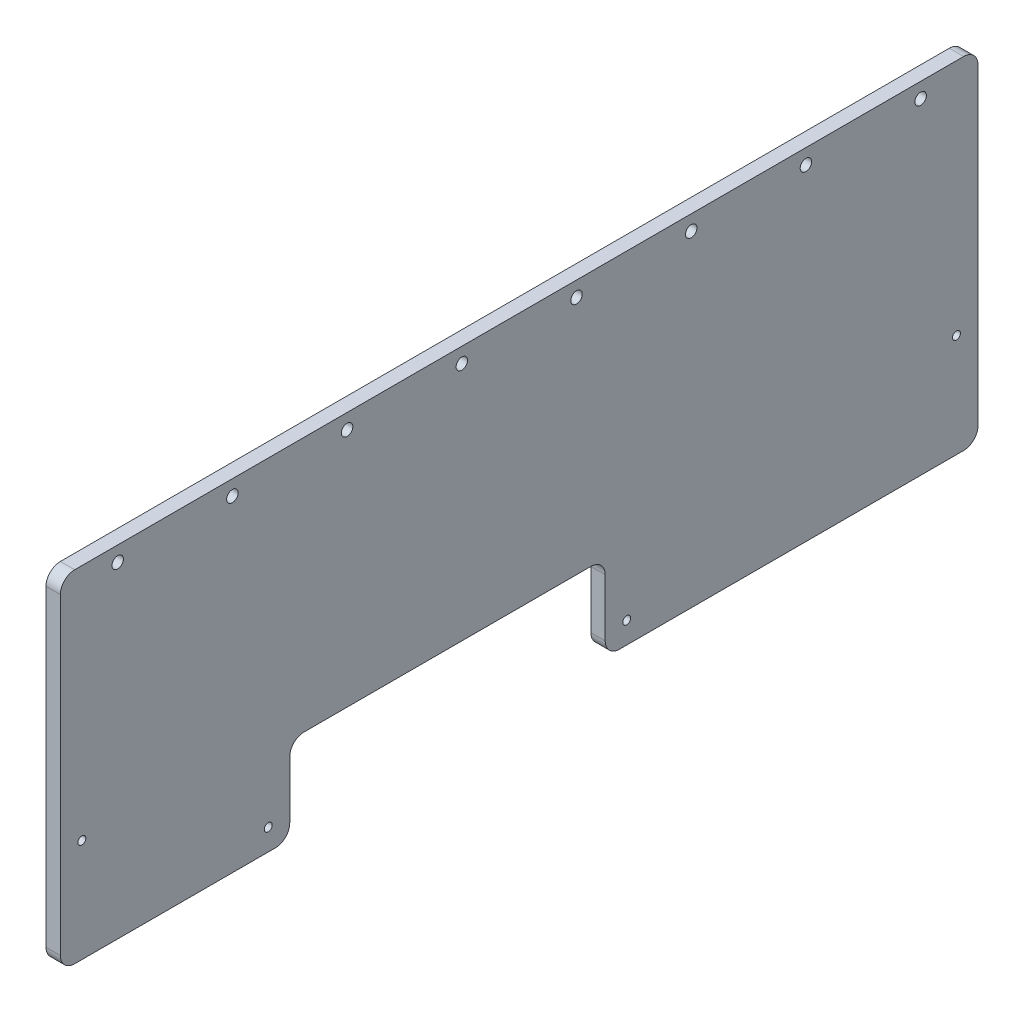
SolidWorks part; units mm, degrees
material "Acrylic (Medium-high impact)"
ref_plane "Front Plane" through (0, 0, 0) normal (0, 0, 1) x (1, 0, 0)
ref_plane "Top Plane" through (0, 0, 0) normal (0, 1, 0) x (1, 0, 0)
ref_plane "Right Plane" through (0, 0, 0) normal (1, 0, 0) x (0, 0, -1)
sketch "Sketch2" plane through (0, 0, 0) normal (1, 0, 0) x (0, 0, -1)
  line L0 (0, 0) -> (0, 294.4501)
  line L1 (0, 294.4501) -> (215.9, 419.1)
  line L2 (215.9, 419.1) -> (431.8, 419.1)
  line L3 (431.8, 419.1) -> (431.8, 0)
  line L4 (431.8, 0) -> (241.3, 0)
  line L5 (241.3, 0) -> (241.3, 38.1)
  line L6 (241.3, 38.1) -> (127, 38.1)
  line L7 (127, 38.1) -> (127, 0)
  line L8 (127, 0) -> (0, 0)
  dimension "D1" = 431.8
  dimension "D2" = 419.1
  dimension "D3" = 127
  dimension "D4" = 114.3
  dimension "D5" = 38.1
  dimension "D6" = 215.9
  dimension "D7" = 150
extrude "Boss-Extrude1" add sketch "Sketch2" along normal blind 6.35 contours L1 L2 L3 L4 L5 L6 L7 L8 L0
sketch "Sketch3" plane through (6.35, 0, 0) normal (1, 0, 0) x (0, 0, -1)
  line L0 (0, 38.1) -> (431.8, 38.1) construction
  line L1 (0, 0) -> (0, 294.4501) construction
  line L2 (431.8, 419.1) -> (431.8, 0) construction
  circle A0 centre (63.5, 38.1) radius 3.9687
  circle A1 centre (368.3, 38.1) radius 3.9688
  dimension "D4" = 7.9375
  dimension "D5" = 7.9375
  dimension "D1" = 38.1
  dimension "D2" = 63.5
  dimension "D3" = 63.5
extrude "Cut-Extrude1" cut sketch "Sketch3" against normal through all
sketch "Sketch4" plane through (6.35, 0, 0) normal (1, 0, 0) x (0, 0, -1)
  line L0 (431.8, 419.1) -> (431.8, 0) construction
  line L1 (215.9, 419.1) -> (431.8, 419.1) construction
  line L2 (393.7, 400.05) -> (393.7, 19.05) construction
  line L4 (393.7, 400.05) -> (330.2, 400.05) construction
  line L5 (330.2, 400.05) -> (330.2, 19.05) construction
  line L6 (330.2, 400.05) -> (330.2, 19.05) construction
  line L7 (330.2, 400.05) -> (323.5506, 19.108) construction
  circle A0 centre (393.7, 400.05) radius 3.175 construction
  circle A1 centre (393.7, 19.05) radius 3.175 construction
  circle A2 centre (323.5506, 19.108) radius 3.175 construction
  circle A3 centre (316.9033, 19.2821) radius 3.175 construction
  circle A4 centre (330.2, 400.05) radius 3.175 construction
  circle A5 centre (330.2, 19.05) radius 3.175 construction
  circle A6 centre (310.26, 19.5721) radius 3.175 construction
  circle A7 centre (303.6228, 19.9781) radius 3.175 construction
  circle A8 centre (296.9937, 20.4998) radius 3.175 construction
  circle A9 centre (290.3747, 21.1372) radius 3.175 construction
  circle A10 centre (283.7678, 21.8899) radius 3.175 construction
  circle A11 centre (277.175, 22.7579) radius 3.175 construction
  circle A12 centre (270.5985, 23.7407) radius 3.175 construction
  dimension "D1" = 6.35
  dimension "D2" = 38.1
  dimension "D3" = 19.05
  dimension "D4" = 381
  dimension "D5" = 10
  dimension "D6" = 1
  dimension "D7" = 101.6
sketch "Sketch5" plane through (6.35, 0, 0) normal (1, 0, 0) x (0, 0, -1)
  line L0 (431.8, 419.1) -> (431.8, 0) construction
  line L1 (431.8, 12.7) -> (425.45, 12.7)
  line L2 (431.8, 12.7) -> (431.8, 25.4)
  line L3 (431.8, 25.4) -> (425.45, 25.4)
  line L4 (425.45, 12.7) -> (425.45, 25.4)
  line L5 (431.8, 0) -> (241.3, 0) construction
  dimension "D1" = 6.35
  dimension "D2" = 12.7
  dimension "D3" = 12.7
extrude "Cut-Extrude3" cut sketch "Sketch5" against normal through all
pattern_linear "LPattern1" count 16 spacing 25.4 along (0, 1, 0) of "Cut-Extrude3"
sketch "Sketch6" plane through (6.35, 0, 0) normal (1, 0, 0) x (0, 0, -1)
  line L0 (0, 0) -> (0, 294.4501) construction
  line L1 (0, 12.7) -> (6.35, 12.7)
  line L2 (0, 12.7) -> (0, 25.4)
  line L3 (0, 25.4) -> (6.35, 25.4)
  line L4 (6.35, 12.7) -> (6.35, 25.4)
  line L5 (425.45, 12.7) -> (431.8, 12.7) construction
  line L6 (425.45, 25.4) -> (425.45, 12.7) construction
  line L7 (127, 0) -> (0, 0) construction
  dimension "D1" = 12.7
extrude "Cut-Extrude4" cut sketch "Sketch6" against normal through all
pattern_linear "LPattern2" count 11 spacing 25.4 along (0, 1, 0) of "Cut-Extrude4"
sketch "Sketch7" plane through (6.35, 0, 0) normal (1, 0, 0) x (0, 0, -1)
  line L0 (127, 38.1) -> (127, 0) construction
  line L1 (127, 12.7) -> (120.65, 12.7)
  line L2 (127, 12.7) -> (127, 25.4)
  line L3 (127, 25.4) -> (120.65, 25.4)
  line L4 (120.65, 12.7) -> (120.65, 25.4)
  line L5 (241.3, 38.1) -> (127, 38.1) construction
  line L6 (127, 38.1) -> (139.7, 38.1)
  line L7 (127, 38.1) -> (127, 44.45)
  line L8 (127, 44.45) -> (139.7, 44.45)
  line L9 (139.7, 38.1) -> (139.7, 44.45)
  line L10 (241.3, 0) -> (241.3, 38.1) construction
  line L11 (152.4, 38.1) -> (165.1, 38.1)
  line L12 (152.4, 38.1) -> (152.4, 44.45)
  line L13 (152.4, 44.45) -> (165.1, 44.45)
  line L14 (165.1, 38.1) -> (165.1, 44.45)
  line L15 (177.8, 38.1) -> (190.5, 38.1)
  line L16 (177.8, 38.1) -> (177.8, 44.45)
  line L17 (177.8, 44.45) -> (190.5, 44.45)
  line L18 (190.5, 38.1) -> (190.5, 44.45)
  line L19 (241.3, 25.4) -> (247.65, 25.4)
  line L20 (241.3, 25.4) -> (241.3, 12.7)
  line L21 (241.3, 12.7) -> (247.65, 12.7)
  line L22 (247.65, 25.4) -> (247.65, 12.7)
  line L23 (0, 12.7) -> (6.35, 12.7) construction
  line L24 (6.35, 12.7) -> (6.35, 25.4) construction
  line L25 (127, 0) -> (0, 0) construction
  line L26 (431.8, 0) -> (241.3, 0) construction
  line L27 (203.2, 44.45) -> (215.9, 44.45)
  line L28 (203.2, 44.45) -> (203.2, 38.1)
  line L29 (203.2, 38.1) -> (215.9, 38.1)
  line L30 (215.9, 44.45) -> (215.9, 38.1)
  line L32 (241.3, 38.1) -> (228.6, 38.1)
  line L33 (241.3, 38.1) -> (241.3, 44.45)
  line L34 (241.3, 44.45) -> (228.6, 44.45)
  line L35 (228.6, 38.1) -> (228.6, 44.45)
  dimension "D1" = 12.7
  dimension "D2" = 12.7
  dimension "D4" = 12.7
  dimension "D5" = 12.7
  dimension "D6" = 12.7
extrude "Cut-Extrude5" cut sketch "Sketch7" against normal through all
sketch "Sketch8" plane through (6.35, 0, 0) normal (1, 0, 0) x (0, 0, -1)
  line L0 (201.9351, 411.0373) -> (212.9336, 417.3873)
  line L1 (201.9351, 411.0373) -> (205.1101, 405.5381)
  line L2 (212.9336, 417.3873) -> (216.1086, 411.8881)
  line L3 (205.1101, 405.5381) -> (216.1086, 411.8881)
  line L4 (0, 294.4501) -> (215.9, 419.1) construction
  line L5 (6.35, 279.4) -> (0, 279.4) construction
  line L6 (6.35, 266.7) -> (6.35, 279.4) construction
  line L7 (216.1086, 411.8881) -> (7.1367, 291.2381) construction
  line L8 (6.35, 279.4) -> (6.35, 292.1) construction
  line L9 (215.9, 412.75) -> (215.6832, 412.6248) construction
  line L10 (7.1367, 291.2381) -> (3.9617, 296.7373) construction
  line L11 (6.35, 292.1) -> (6.5668, 292.2252) construction
  line L12 (215.9, 419.1) -> (215.9, 412.75) construction
  line L13 (215.9, 419.1) -> (431.8, 419.1) construction
  dimension "D1" = 215.9
  dimension "D2" = 241.3
  dimension "D3" = 6.35
extrude "Cut-Extrude6" cut sketch "Sketch8" against normal through all
pattern_linear "LPattern3" count 10 spacing 25.4 along (0, -0.5, 0.866) of "Cut-Extrude6"
sketch "Sketch9" plane through (6.35, 0, 0) normal (1, 0, 0) x (0, 0, -1)
  line L0 (215.9, 419.1) -> (431.8, 419.1) construction
  line L1 (419.1, 419.1) -> (406.4, 419.1)
  line L2 (419.1, 419.1) -> (419.1, 412.75)
  line L3 (419.1, 412.75) -> (406.4, 412.75)
  line L4 (406.4, 419.1) -> (406.4, 412.75)
  line L5 (431.8, 406.4) -> (425.45, 406.4) construction
  line L6 (425.45, 406.4) -> (425.45, 393.7) construction
  line L7 (431.8, 419.1) -> (431.8, 406.4) construction
  dimension "D1" = 12.7
extrude "Cut-Extrude7" cut sketch "Sketch9" against normal through all
pattern_linear "LPattern4" count 8 spacing 25.4 along (0, 0, 1) of "Cut-Extrude7"
sketch "Sketch10" plane through (6.35, 0, 0) normal (1, 0, 0) x (0, 0, -1)
  line L0 (127, 0) -> (0, 0) construction
  line L1 (146.05, 273.05) -> (222.25, 273.05) construction
  line L2 (146.05, 273.05) -> (146.05, 57.15) construction
  line L3 (146.05, 57.15) -> (222.25, 57.15) construction
  line L4 (222.25, 273.05) -> (222.25, 57.15) construction
  line L5 (146.05, 273.05) -> (19.05, 273.05) construction
  line L6 (146.05, 273.05) -> (146.05, 247.65) construction
  line L7 (146.05, 247.65) -> (19.05, 247.65) construction
  line L8 (19.05, 273.05) -> (19.05, 247.65) construction
  line L9 (0, 254) -> (0, 266.7) construction
  line L10 (127, 44.45) -> (127, 25.4) construction
  line L11 (241.3, 25.4) -> (241.3, 44.45) construction
  line L12 (152.4, 38.1) -> (139.7, 38.1) construction
  circle A0 centre (222.25, 273.05) radius 3.175
  circle A1 centre (222.25, 57.15) radius 3.175
  circle A2 centre (146.05, 57.15) radius 3.175
  circle A3 centre (146.05, 273.05) radius 3.175
  circle A4 centre (19.05, 273.05) radius 3.175 construction
  circle A5 centre (19.05, 247.65) radius 3.175 construction
  circle A6 centre (146.05, 247.65) radius 3.175 construction
  dimension "D4" = 6.35
  dimension "D1" = 273.05
  dimension "D2" = 19.05
  dimension "D3" = 247.65
  dimension "D5" = 19.05
  dimension "D6" = 19.05
  dimension "D7" = 19.05
extrude "Cut-Extrude8" cut sketch "Sketch10" against normal through all
sketch "Sketch11" plane through (6.35, 0, 0) normal (1, 0, 0) x (0, 0, -1)
  line L0 (127, 0) -> (0, 0) construction
  line L1 (0, 254) -> (0, 266.7) construction
  line L5 (241.3, 0) -> (241.3, 12.7) construction
  line L6 (177.8, 38.1) -> (165.1, 38.1) construction
  line L7 (38.1, 260.35) -> (266.7, 260.35) construction
  line L8 (266.7, 260.35) -> (266.7, 63.5) construction
  circle A0 centre (38.1, 260.35) radius 3.9688
  circle A1 centre (266.7, 63.5) radius 3.9688 construction
  circle A2 centre (266.7, 260.35) radius 3.9688
  dimension "D3" = 7.9375
  dimension "D1" = 260.35
  dimension "D2" = 38.1
  dimension "D4" = 25.4
  dimension "D5" = 25.4
extrude "Cut-Extrude9" cut sketch "Sketch11" against normal through all
sketch "Sketch12" plane through (6.35, 0, 0) normal (1, 0, 0) x (0, 0, -1)
  line L0 (127, 50.8) -> (127, 38.1)
  line L1 (120.65, 25.4) -> (127, 25.4)
  line L2 (120.65, 25.4) -> (120.65, 12.7)
  line L3 (120.65, 12.7) -> (127, 12.7)
  line L4 (127, 25.4) -> (127, 12.7)
  line L5 (120.65, 50.8) -> (127, 50.8)
  line L6 (120.65, 50.8) -> (120.65, 38.1)
  line L7 (120.65, 38.1) -> (127, 38.1)
  line L8 (127, 76.2) -> (127, 63.5)
  line L9 (120.65, 76.2) -> (127, 76.2)
  line L10 (120.65, 76.2) -> (120.65, 63.5)
  line L11 (120.65, 63.5) -> (127, 63.5)
  line L12 (127, 101.6) -> (127, 88.9)
  line L13 (120.65, 101.6) -> (127, 101.6)
  line L14 (120.65, 101.6) -> (120.65, 88.9)
  line L15 (120.65, 88.9) -> (127, 88.9)
  line L16 (127, 127) -> (127, 114.3)
  line L17 (120.65, 127) -> (127, 127)
  line L18 (120.65, 127) -> (120.65, 114.3)
  line L19 (120.65, 114.3) -> (127, 114.3)
  line L20 (127, 152.4) -> (127, 139.7) construction
  line L21 (120.65, 152.4) -> (127, 152.4) construction
  line L22 (120.65, 152.4) -> (120.65, 139.7) construction
  line L23 (120.65, 139.7) -> (127, 139.7) construction
  line L24 (127, 177.8) -> (127, 165.1) construction
  line L25 (120.65, 177.8) -> (127, 177.8) construction
  line L26 (120.65, 177.8) -> (120.65, 165.1) construction
  line L27 (120.65, 165.1) -> (127, 165.1) construction
  dimension "D1" = 7
extrude "Cut-Extrude13" cut sketch "Sketch12" against normal through all
sketch "Sketch13" plane through (6.35, 0, 0) normal (1, 0, 0) x (0, 0, -1)
  line L1 (120.65, 25.4) -> (120.65, 12.7) construction
  line L2 (84.65, 117.2) -> (347.15, 117.2) construction
  line L3 (84.65, 117.2) -> (6.35, 117.2) construction
  line L4 (6.35, 114.3) -> (6.35, 127) construction
  line L5 (347.15, 117.2) -> (425.45, 117.2) construction
  line L6 (425.45, 127) -> (425.45, 114.3) construction
  circle A0 centre (84.65, 117.2) radius 20
  circle A1 centre (347.15, 117.2) radius 20
  dimension "D2" = 40
  dimension "D1" = 9.8
  dimension "D3" = 36
sketch "Sketch14" plane through (6.35, 0, 0) normal (1, 0, 0) x (0, 0, -1)
  line L0 (36.9572, 315.7873) -> (47.9558, 322.1373)
  line L1 (36.9572, 315.7873) -> (40.1322, 310.2881)
  line L2 (47.9558, 322.1373) -> (51.1308, 316.6381)
  line L3 (40.1322, 310.2881) -> (51.1308, 316.6381)
  line L4 (80.9513, 341.1873) -> (91.9498, 347.5373)
  line L5 (80.9513, 341.1873) -> (84.1263, 335.6881)
  line L6 (91.9498, 347.5373) -> (95.1248, 342.0381)
  line L7 (84.1263, 335.6881) -> (95.1248, 342.0381)
  line L8 (91.9498, 347.5373) -> (95.1248, 342.0381) construction
extrude "Cut-Extrude15" cut sketch "Sketch14" against normal through all
sketch "Sketch15" plane through (6.35, 0, 0) normal (1, 0, 0) x (0, 0, -1)
  line L0 (43.8866, 319.2853) -> (85.4558, 343.2853) construction
  line L1 (46.8439, 314.1631) -> (53.1939, 303.1646) construction
  line L3 (64.6712, 331.2853) -> (64.4535, 331.6623) construction
  line L4 (58.9543, 328.4873) -> (69.9528, 334.8373) construction
  line L5 (29.1337, 303.9381) -> (62.1293, 322.9881) construction
  line L6 (31.5586, 305.3381) -> (62.1293, 322.9881)
  line L7 (73.1278, 329.3381) -> (103.6985, 346.9881)
  line L8 (73.1278, 329.3381) -> (106.1234, 348.3881) construction
  circle A0 centre (43.8866, 319.2853) radius 18.6147
  circle A1 centre (85.4558, 343.2853) radius 18.6147
  dimension "D2" = 12.7
  dimension "D1" = 48
extrude "Cut-Extrude16" cut sketch "Sketch15" against normal through all contours L6 A0 | L7 A1
sketch "Sketch17" plane through (6.35, 0, 0) normal (1, 0, 0) x (0, 0, -1)
  line L0 (0, 139.7) -> (6.35, 139.7) construction
  line L1 (19.05, 146.05) -> (31.75, 146.05)
  line L2 (19.05, 146.05) -> (19.05, 139.7)
  line L3 (19.05, 139.7) -> (31.75, 139.7)
  line L4 (31.75, 146.05) -> (31.75, 139.7)
  line L5 (6.35, 139.7) -> (6.35, 152.4) construction
  dimension "D1" = 12.7
  dimension "D2" = 6.35
  dimension "D3" = 12.7
extrude "Cut-Extrude17" cut sketch "Sketch17" against normal through all
pattern_linear "LPattern5" count 17 spacing 25.4 along (0, 0, -1) of "Cut-Extrude17"
pattern_linear "LPattern6" count 2 spacing 120.65 along (0, 0, -1) of "Cut-Extrude13"
sketch "Sketch18" plane through (6.35, 0, 0) normal (1, 0, 0) x (0, 0, -1)
  line L1 (127, 120.65) -> (139.7, 120.65)
  line L2 (127, 120.65) -> (127, 114.3)
  line L3 (127, 114.3) -> (139.7, 114.3)
  line L4 (139.7, 120.65) -> (139.7, 114.3)
  dimension "D1" = 12.7
  dimension "D2" = 6.35
extrude "Cut-Extrude18" cut sketch "Sketch18" against normal through all
pattern_linear "LPattern7" count 5 spacing 25.4 along (0, 0, -1) of "Cut-Extrude18"
sketch "Sketch19" plane through (6.35, 0, 0) normal (1, 0, 0) x (0, 0, -1)
  line L0 (25.4, 279.7854) -> (222.7059, 393.7)
  line L1 (222.7059, 393.7) -> (406.4, 393.7)
  line L2 (406.4, 393.7) -> (406.4, 165.1)
  line L3 (406.4, 165.1) -> (25.4, 165.1)
  line L4 (25.4, 165.1) -> (25.4, 279.7854)
  line L5 (0, 228.6) -> (0, 241.3) construction
  line L6 (431.8, 292.1) -> (431.8, 279.4) construction
  line L7 (368.3, 419.1) -> (381, 419.1) construction
  line L9 (146.9425, 379.2873) -> (157.941, 385.6373) construction
  line L10 (124.9454, 366.5873) -> (135.9439, 372.9373) construction
  line L11 (222.25, 139.7) -> (234.95, 139.7) construction
  point P16 (130.4447, 369.7623)
  dimension "D1" = 25.4
  dimension "D2" = 25.4
  dimension "D3" = 25.4
  dimension "D4" = 25.4
  dimension "D5" = 25.4
extrude "Cut-Extrude19" cut sketch "Sketch19" against normal through all
sketch "Sketch20" plane through (6.35, 0, 0) normal (1, 0, 0) x (0, 0, -1)
  line L0 (165.1, 120.65) -> (152.4, 120.65) construction
  line L1 (133.35, 107.95) -> (234.95, 107.95)
  line L2 (133.35, 107.95) -> (133.35, 50.8)
  line L3 (133.35, 50.8) -> (234.95, 50.8)
  line L4 (234.95, 107.95) -> (234.95, 50.8)
  line L5 (120.65, 101.6) -> (120.65, 88.9) construction
  line L6 (177.8, 38.1) -> (165.1, 38.1) construction
  line L7 (247.65, 101.6) -> (247.65, 88.9) construction
  dimension "D1" = 12.7
  dimension "D2" = 12.7
  dimension "D3" = 12.7
  dimension "D4" = 12.7
extrude "Cut-Extrude20" cut sketch "Sketch20" against normal through all
sketch "Sketch21" plane through (6.35, 0, 0) normal (1, 0, 0) x (0, 0, -1)
  line L0 (266.7, 25.4) -> (308.203, 25.4)
  line L1 (25.4, 133.35) -> (25.4, 82.0941)
  line L2 (308.203, 25.4) -> (406.4, 82.0941)
  line L3 (25.4, 82.0941) -> (101.6, 38.1)
  line L4 (406.4, 82.0941) -> (406.4, 133.35)
  line L5 (406.4, 133.35) -> (266.7, 133.35)
  line L6 (266.7, 133.35) -> (266.7, 25.4)
  line L7 (406.4, 165.1) -> (406.4, 393.7) construction
  line L8 (431.8, 0) -> (241.3, 0) construction
  line L9 (241.3, 25.4) -> (241.3, 38.1) construction
  line L10 (387.35, 146.05) -> (374.65, 146.05) construction
  line L11 (101.6, 38.1) -> (101.6, 133.35)
  line L12 (101.6, 133.35) -> (25.4, 133.35)
  line L13 (0, 101.6) -> (0, 114.3) construction
  line L14 (127, 101.6) -> (127, 88.9) construction
  line L20 (25.4, 38.1) -> (25.4, 25.4)
  line L21 (25.4, 25.4) -> (47.397, 25.4)
  line L22 (47.397, 25.4) -> (25.4, 38.1)
  circle A0 centre (63.5, 38.1) radius 3.9687 construction
  circle A1 centre (368.3, 38.1) radius 3.9688 construction
  dimension "D4" = 150
  dimension "D5" = 19.05
  dimension "D9" = 19.05
  dimension "D1" = 25.4
  dimension "D2" = 25.4
  dimension "D3" = 12.7
  dimension "D6" = 25.4
  dimension "D7" = 25.4
  dimension "D8" = 120
  dimension "D12" = 19.05
extrude "Cut-Extrude21" cut sketch "Sketch21" against normal through all
sketch "Sketch22" plane through (6.35, 0, 0) normal (1, 0, 0) x (0, 0, -1)
  line L0 (384.403, 25.4) -> (406.4, 38.1)
  line L1 (406.4, 38.1) -> (406.4, 25.4)
  line L2 (406.4, 25.4) -> (384.403, 25.4)
  line L3 (406.4, 82.0941) -> (406.4, 133.35) construction
  line L4 (266.7, 25.4) -> (308.203, 25.4) construction
  line L5 (358.775, 54.5978) -> (377.825, 21.6022) construction
  line L6 (308.203, 25.4) -> (406.4, 82.0941) construction
  point P11 (368.3, 38.1)
extrude "Cut-Extrude22" cut sketch "Sketch22" against normal through all
sketch "Sketch26" plane through (6.35, 0, 0) normal (1, 0, 0) x (0, 0, -1)
  line L0 (278.9441, 133.35) -> (234.95, 107.95) construction
  line L1 (278.9441, 133.35) -> (275.7691, 138.8493) construction
  line L2 (234.95, 107.95) -> (231.775, 113.4493) construction
  line L3 (275.7691, 138.8493) -> (231.775, 113.4493) construction
  line L4 (406.4, 133.35) -> (266.7, 133.35) construction
  line L5 (228.6, 120.65) -> (228.6, 114.3) construction
  line L6 (308.203, 25.4) -> (406.4, 82.0941) construction
  line L7 (266.7, 133.35) -> (266.7, 126.2809)
  line L8 (266.7, 133.35) -> (266.7, 25.4) construction
  line L9 (266.7, 126.2809) -> (278.9441, 133.35)
  line L10 (278.9441, 133.35) -> (266.7, 133.35)
  line L11 (89.3559, 133.35) -> (101.6, 126.2809)
  line L12 (101.6, 133.35) -> (25.4, 133.35) construction
  line L13 (101.6, 38.1) -> (101.6, 133.35) construction
  line L14 (101.6, 126.2809) -> (101.6, 133.35)
  line L15 (101.6, 133.35) -> (89.3559, 133.35)
  line L16 (25.4, 82.0941) -> (101.6, 38.1) construction
  line L17 (266.7, 32.4691) -> (278.9441, 25.4)
  line L18 (266.7, 133.35) -> (266.7, 25.4) construction
  line L19 (266.7, 25.4) -> (308.203, 25.4) construction
  line L20 (278.9441, 25.4) -> (266.7, 25.4)
  line L21 (266.7, 25.4) -> (266.7, 32.4691)
  line L22 (133.35, 107.95) -> (133.35, 100.8809)
  line L23 (133.35, 107.95) -> (133.35, 50.8) construction
  line L24 (133.35, 100.8809) -> (145.5941, 107.95)
  line L25 (234.95, 107.95) -> (133.35, 107.95) construction
  line L26 (145.5941, 107.95) -> (133.35, 107.95)
  line L27 (234.95, 107.95) -> (222.7059, 107.95)
  line L28 (222.7059, 107.95) -> (234.95, 100.8809)
  line L29 (234.95, 50.8) -> (234.95, 107.95) construction
  line L30 (234.95, 100.8809) -> (234.95, 107.95)
  line L31 (133.35, 50.8) -> (145.5941, 50.8)
  line L32 (133.35, 50.8) -> (234.95, 50.8) construction
  line L33 (145.5941, 50.8) -> (133.35, 57.8691)
  line L34 (133.35, 57.8691) -> (133.35, 50.8)
  line L35 (234.95, 50.8) -> (222.7059, 50.8)
  line L36 (222.7059, 50.8) -> (234.95, 57.8691)
  line L37 (234.95, 57.8691) -> (234.95, 50.8)
extrude "Boss-Extrude4" add sketch "Sketch26" against normal through all
sketch "Sketch27" plane through (6.35, 0, 0) normal (1, 0, 0) x (0, 0, -1)
  line L0 (12.7, 163.83) -> (12.7, 12.7)
  line L1 (12.7, 12.7) -> (114.3, 12.7)
  line L2 (114.3, 12.7) -> (114.3, 50.8)
  line L3 (114.3, 50.8) -> (254, 50.8)
  line L4 (254, 50.8) -> (254, 12.7)
  line L5 (254, 12.7) -> (419.1, 12.7)
  line L6 (419.1, 12.7) -> (419.1, 163.83)
  line L7 (419.1, 163.83) -> (12.7, 163.83)
  line L8 (0, 101.6) -> (0, 114.3) construction
  line L9 (127, 0) -> (0, 0) construction
  line L10 (127, 38.1) -> (127, 25.4) construction
  line L11 (177.8, 38.1) -> (165.1, 38.1) construction
  line L12 (241.3, 25.4) -> (241.3, 38.1) construction
  line L13 (431.8, 0) -> (241.3, 0) construction
  line L14 (431.8, 63.5) -> (431.8, 50.8) construction
  line L15 (31.75, 146.05) -> (19.05, 146.05) construction
  point P12 (127, 31.75)
  dimension "D1" = 12.7
  dimension "D2" = 12.7
  dimension "D3" = 12.7
  dimension "D4" = 12.7
  dimension "D5" = 12.7
  dimension "D6" = 12.7
  dimension "D7" = 12.7
  dimension "D8" = 17.78
extrude "Boss-Extrude5" add sketch "Sketch27" against normal blind 6.35 separate body
sketch "Sketch29" plane through (6.35, 0, 0) normal (1, 0, 0) x (0, 0, -1)
  line L0 (12.7, 157.1625) -> (419.1, 157.1625) construction
  line L1 (12.7, 163.83) -> (12.7, 12.7) construction
  line L2 (419.1, 12.7) -> (419.1, 163.83) construction
  line L4 (25.4, 165.1) -> (406.4, 165.1) construction
  circle A0 centre (38.1, 157.1625) radius 2.54
  circle A2 centre (88.9, 157.1625) radius 2.54
  circle A4 centre (139.7, 157.1625) radius 2.54
  circle A6 centre (190.5, 157.1625) radius 2.54
  circle A8 centre (241.3, 157.1625) radius 2.54
  circle A10 centre (292.1, 157.1625) radius 2.54
  circle A12 centre (342.9, 157.1625) radius 2.54
  circle A14 centre (393.7, 157.1625) radius 2.54
  circle A16 centre (63.5, 157.1625) radius 2.54 [skipped]
  circle A17 centre (114.3, 157.1625) radius 2.54 [skipped]
  circle A18 centre (165.1, 157.1625) radius 2.54 [skipped]
  circle A19 centre (215.9, 157.1625) radius 2.54 [skipped]
  circle A20 centre (266.7, 157.1625) radius 2.54 [skipped]
  circle A21 centre (317.5, 157.1625) radius 2.54 [skipped]
  circle A22 centre (368.3, 157.1625) radius 2.54 [skipped]
  circle A23 centre (419.1, 157.1625) radius 2.54 [skipped]
  dimension "D3" = 5.08
  dimension "D1" = 7.9375
  dimension "D2" = 25.4
  dimension "D4" = 16
extrude "Cut-Extrude23" cut sketch "Sketch29" against normal through all
sketch "Sketch30" plane through (6.35, 0, 0) normal (1, 0, 0) x (0, 0, -1)
  line L0 (12.7, 12.7) -> (114.3, 12.7) construction
  line L1 (12.7, 163.83) -> (12.7, 12.7) construction
  line L2 (254, 12.7) -> (419.1, 12.7) construction
  line L3 (419.1, 12.7) -> (419.1, 163.83) construction
  line L4 (254, 50.8) -> (254, 12.7) construction
  line L5 (114.3, 12.7) -> (114.3, 50.8) construction
  circle A0 centre (22.225, 58.42) radius 1.75
  circle A1 centre (104.775, 22.225) radius 1.75
  circle A2 centre (263.525, 22.225) radius 1.75
  circle A3 centre (409.575, 58.42) radius 1.75
  dimension "D9" = 3.5
  dimension "D1" = 45.72
  dimension "D2" = 9.525
  dimension "D3" = 9.525
  dimension "D4" = 9.525
  dimension "D5" = 45.72
  dimension "D6" = 9.525
  dimension "D7" = 9.525
  dimension "D8" = 9.525
extrude "Cut-Extrude24" cut sketch "Sketch30" against normal through all
delete or keep bodies "Body-Delete1" type delete bodies bodies 130
fillet "Fillet2" radius 6.35 8 edges at (3.175, 163.83, -12.7) (3.175, 163.83, -419.1) (3.175, 12.7, -419.1) (3.175, 50.8, -254) (3.175, 12.7, -254) (3.175, 50.8, -114.3) (3.175, 12.7, -114.3) (3.175, 12.7, -12.7)
